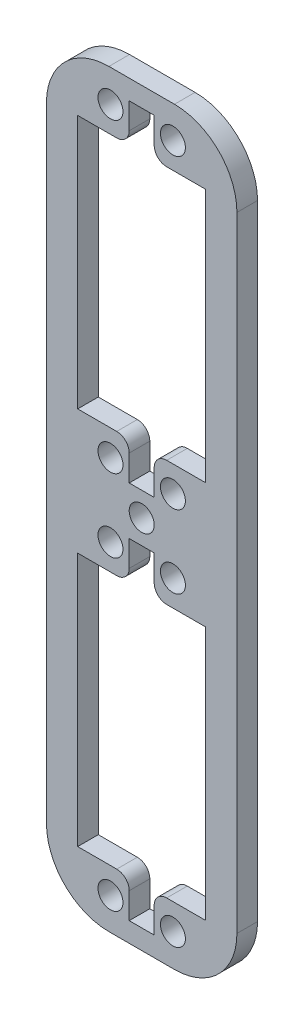
SolidWorks part; units mm, degrees
material "1060 Alloy"
ref_plane "Front Plane" through (0, 0, 0) normal (0, 0, 1) x (1, 0, 0)
ref_plane "Top Plane" through (0, 0, 0) normal (0, 1, 0) x (1, 0, 0)
ref_plane "Right Plane" through (0, 0, 0) normal (1, 0, 0) x (0, 0, -1)
sketch "Sketch2" plane through (0, 0, 0) normal (0, 0, 1) x (1, 0, 0)
  line L0 (0, 0) -> (-15.25, 0) construction
  line L1 (-5.25, -60) -> (5.25, -60)
  line L2 (-15.25, -50) -> (-15.25, 50)
  line L3 (-5.25, 60) -> (5.25, 60)
  line L4 (15.25, -50) -> (15.25, 50)
  line L5 (-15.25, -60) -> (15.25, 60) construction
  line L6 (-15.25, 60) -> (15.25, -60) construction
  line L7 (-10.25, 50.7) -> (-4, 50.7)
  line L8 (-10.25, 50.7) -> (-10.25, 10)
  line L9 (-10.25, 10) -> (-4, 10)
  line L10 (10.25, 50.7) -> (10.25, 10)
  line L11 (-10.25, 50.7) -> (10.25, 10) construction
  line L12 (-10.25, 10) -> (10.25, 50.7) construction
  line L13 (4, 50.7) -> (10.25, 50.7)
  line L14 (-10.25, -50.7) -> (-4, -50.7)
  line L15 (10.25, -50.7) -> (10.25, -10)
  line L16 (-10.25, -50.7) -> (-10.25, -10)
  line L17 (-10.25, -10) -> (-4, -10)
  line L18 (0, 0) -> (0, 60) construction
  line L19 (0, 30.35) -> (15.25, 30.35) construction
  line L20 (-2, 8) -> (-2, 3.85)
  line L21 (2, 3.85) -> (-2, 3.85)
  line L22 (2, 52.7) -> (2, 56.85)
  line L23 (2, 56.85) -> (-2, 56.85)
  line L24 (-2, 52.7) -> (-2, 56.85)
  line L25 (2, 8) -> (2, 3.85)
  line L26 (4, 10) -> (10.25, 10)
  line L27 (2, -3.85) -> (-2, -3.85)
  line L28 (-2, -8) -> (-2, -3.85)
  line L29 (2, -8) -> (2, -3.85)
  line L30 (-2, -52.7) -> (-2, -56.85)
  line L31 (2, -52.7) -> (2, -56.85)
  line L32 (2, -56.85) -> (-2, -56.85)
  line L33 (4, -10) -> (10.25, -10)
  line L34 (4, -50.7) -> (10.25, -50.7)
  circle A0 centre (0, 0) radius 2
  circle A1 centre (5, 5.85) radius 2
  circle A2 centre (5, -5.85) radius 2
  circle A3 centre (-5, -5.85) radius 2
  circle A4 centre (-5, 5.85) radius 2
  circle A5 centre (5, 54.85) radius 2
  circle A6 centre (5, -54.85) radius 2
  circle A7 centre (-5, -54.85) radius 2
  circle A8 centre (-5, 54.85) radius 2
  arc A9 (5.25, -60) -> (15.25, -50) centre (5.25, -50) ccw
  arc A10 (-5.25, -60) -> (-15.25, -50) centre (-5.25, -50) cw
  arc A11 (5.25, 60) -> (15.25, 50) centre (5.25, 50) cw
  arc A12 (-15.25, 50) -> (-5.25, 60) centre (-5.25, 50) cw
  arc A13 (2, -52.7) -> (4, -50.7) centre (4, -52.7) cw
  arc A14 (-2, -52.7) -> (-4, -50.7) centre (-4, -52.7) ccw
  arc A15 (-2, -8) -> (-4, -10) centre (-4, -8) cw
  arc A16 (2, -8) -> (4, -10) centre (4, -8) ccw
  arc A17 (-2, 8) -> (-4, 10) centre (-4, 8) ccw
  arc A18 (2, 8) -> (4, 10) centre (4, 8) cw
  arc A19 (-4, 50.7) -> (-2, 52.7) centre (-4, 52.7) ccw
  arc A20 (4, 50.7) -> (2, 52.7) centre (4, 52.7) cw
  point P0 (0, 0)
  point P5 (0, 30.35)
  point P54 (0, 56.85)
  point P69 (2, -50.7)
  point P72 (-2, -50.7)
  point P75 (-2, -10)
  point P78 (2, -10)
  point P81 (-2, 10)
  point P84 (2, 10)
  point P87 (-2, 50.7)
  point P90 (2, 50.7)
  dimension "D6" = 4
  dimension "D7" = 10.25
  dimension "D9" = 4
  dimension "D10" = 10
  dimension "D14" = 2
  dimension "D1" = 120
  dimension "D2" = 30.5
  dimension "D3" = 40.7
  dimension "D4" = 20.5
  dimension "D5" = 20
  dimension "D8" = 11.7
  dimension "D11" = 4
  dimension "D12" = 49
  dimension "D13" = 10
extrude "Boss-Extrude1" add sketch "Sketch2" along normal mid plane 3.3
